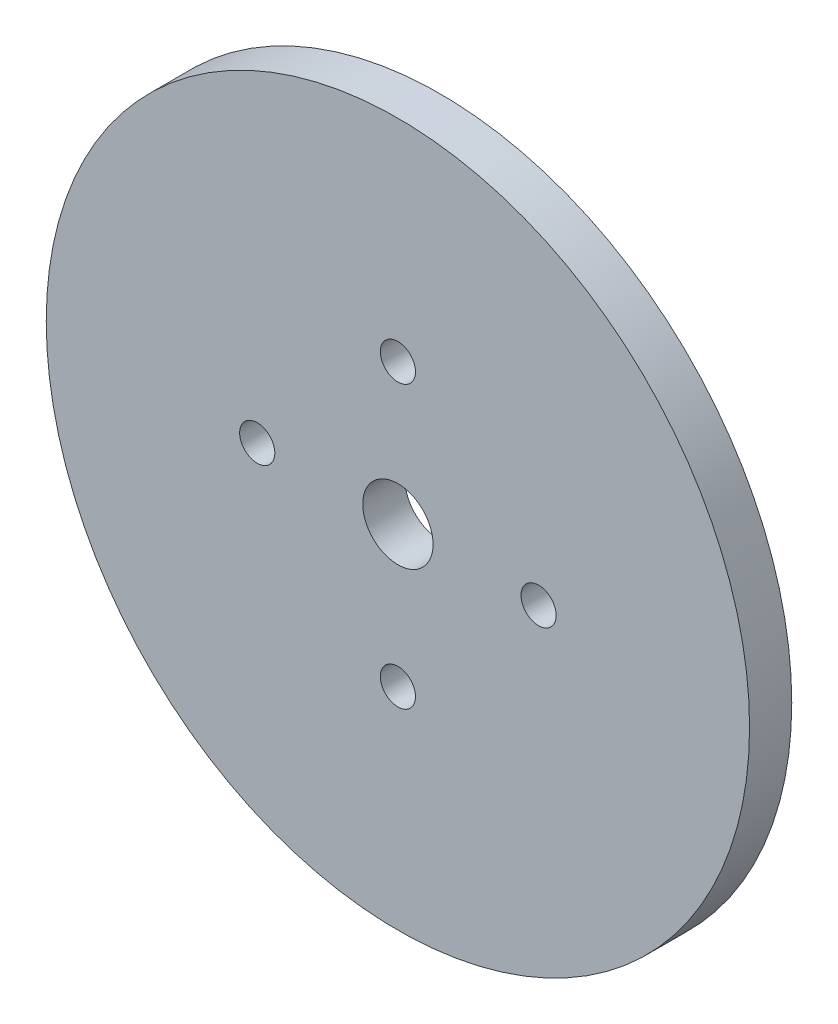
SolidWorks part; units mm, degrees
material "Pine"
ref_plane "Front Plane" through (0, 0, 0) normal (0, 0, 1) x (1, 0, 0)
ref_plane "Top Plane" through (0, 0, 0) normal (0, 1, 0) x (1, 0, 0)
ref_plane "Right Plane" through (0, 0, 0) normal (1, 0, 0) x (0, 0, -1)
sketch "Sketch1" plane through (0, 0, 0) normal (0, 0, 1) x (1, 0, 0)
  circle A0 centre (0, 0) radius 50
  circle A1 centre (0, 0) radius 5
  dimension "D1" = 100
  dimension "D2" = 10
extrude "Boss-Extrude1" add sketch "Sketch1" along normal blind 6
sketch "Sketch2" plane through (0, 0, 0) normal (0, 0, -1) x (-1, 0, 0)
  line L0 (0, 0) -> (0, 32.7517) construction
  circle A0 centre (0, 20) radius 2.5
  circle A1 centre (20, 0) radius 2.5
  circle A2 centre (0, -20) radius 2.5
  circle A3 centre (-20, 0) radius 2.5
  point P14 (0, 0)
  dimension "D1" = 5
  dimension "D2" = 20
  dimension "D3" = 4
extrude "Cut-Extrude1" cut sketch "Sketch2" against normal through all
